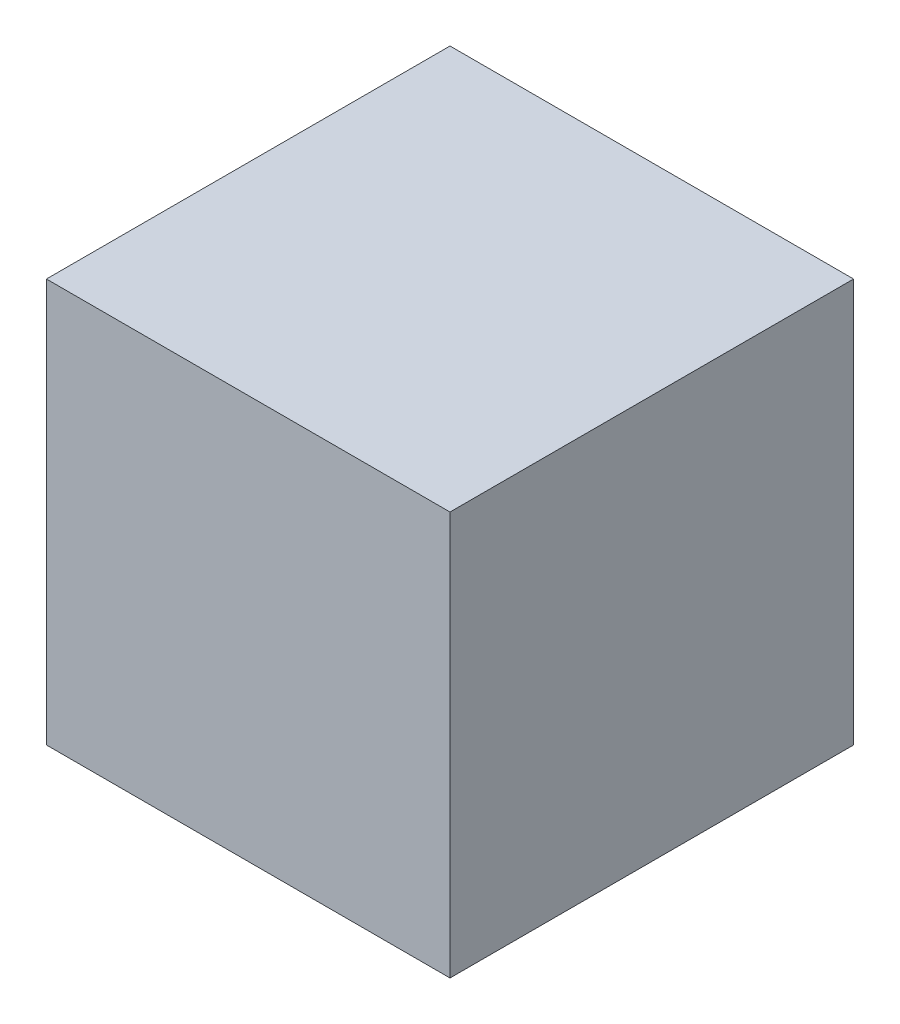
SolidWorks part; units mm, degrees
ref_plane "Front Plane" through (0, 0, 0) normal (0, 0, 1) x (1, 0, 0)
ref_plane "Top Plane" through (0, 0, 0) normal (0, 1, 0) x (1, 0, 0)
ref_plane "Right Plane" through (0, 0, 0) normal (1, 0, 0) x (0, 0, -1)
sketch "Sketch1" plane through (0, 0, 0) normal (0, 1, 0) x (1, 0, 0)
  line L1 (0, 0) -> (100, 0)
  line L2 (0, 0) -> (0, -100)
  line L3 (0, -100) -> (100, -100)
  line L4 (100, 0) -> (100, -100)
  dimension "D1" = 100
  dimension "D2" = 100
extrude "Boss-Extrude1" add sketch "Sketch1" along normal blind 100 contours L2 L1 L4 L3
